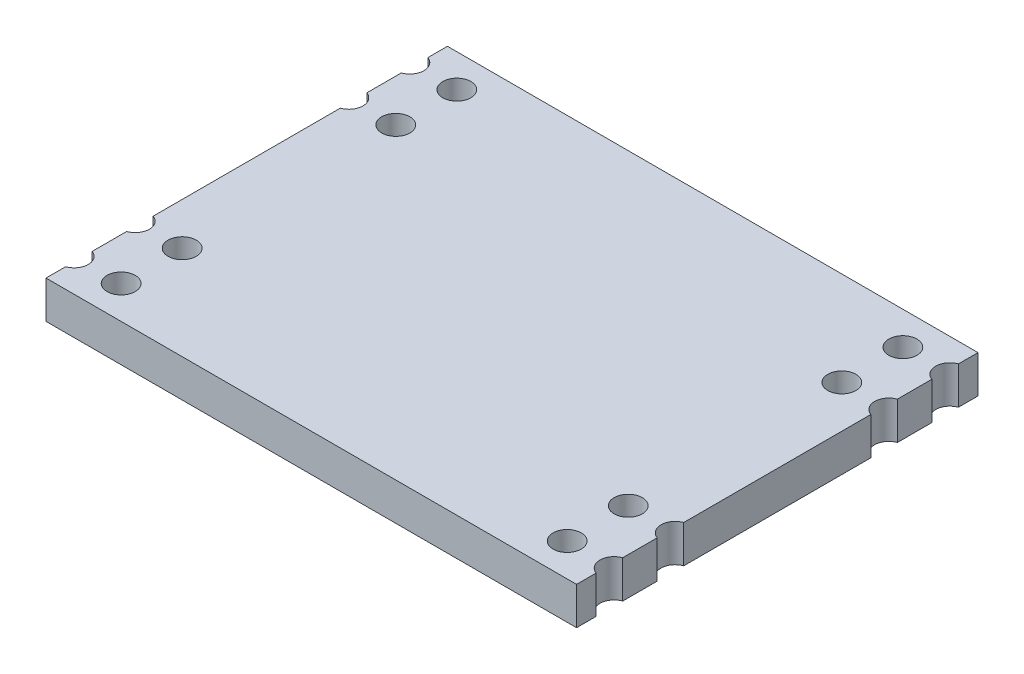
SolidWorks part; units mm, degrees
ref_plane "Front Plane" through (0, 0, 0) normal (0, 0, 1) x (1, 0, 0)
ref_plane "Top Plane" through (0, 0, 0) normal (0, 1, 0) x (1, 0, 0)
ref_plane "Right Plane" through (0, 0, 0) normal (1, 0, 0) x (0, 0, -1)
sketch "Sketch1" plane through (0, 0, 0) normal (0, 1, 0) x (1, 0, 0)
  line L1 (-11.3, 8.55) -> (11.3, 8.55)
  line L2 (-11.3, 8.55) -> (-11.3, -8.55)
  line L3 (-11.3, -8.55) -> (11.3, -8.55)
  line L4 (11.3, 8.55) -> (11.3, -8.55)
  line L5 (-11.3, 8.55) -> (11.3, -8.55) construction
  line L6 (-11.3, -8.55) -> (11.3, 8.55) construction
  point P0 (0, 0)
  dimension "D1" = 17.1
  dimension "D2" = 22.6
extrude "MAIN BODY" add sketch "Sketch1" along normal blind 1.6
sketch "Sketch2" plane through (0, 1.6, 0) normal (0, 1, 0) x (1, 0, 0)
  line L0 (-9.5, 7.15) -> (-9.5, 4.55) construction
  line L1 (11.3, 8.55) -> (-11.3, 8.55) construction
  line L2 (-11.3, 8.55) -> (-11.3, -8.55) construction
  circle A0 centre (-9.5, 7.15) radius 0.6
  circle A1 centre (-9.5, 4.55) radius 0.6
  dimension "D1" = 1.2
  dimension "D2" = 2.6
  dimension "D3" = 1.4
  dimension "D4" = 1.8
extrude "SOLDERED CONNECTION HOLES" cut sketch "Sketch2" against normal through all
pattern_linear "LPattern1" count 2 spacing 2 along (-1, 0, 0) of "SOLDERED CONNECTION HOLES"
mirror "Mirror1" about plane through (0, 0, 0) normal (1, 0, 0) of "LPattern1", "SOLDERED CONNECTION HOLES"
mirror "Mirror2" about plane through (0, 0, 0) normal (0, 0, 1) of "LPattern1", "SOLDERED CONNECTION HOLES", "Mirror1"
